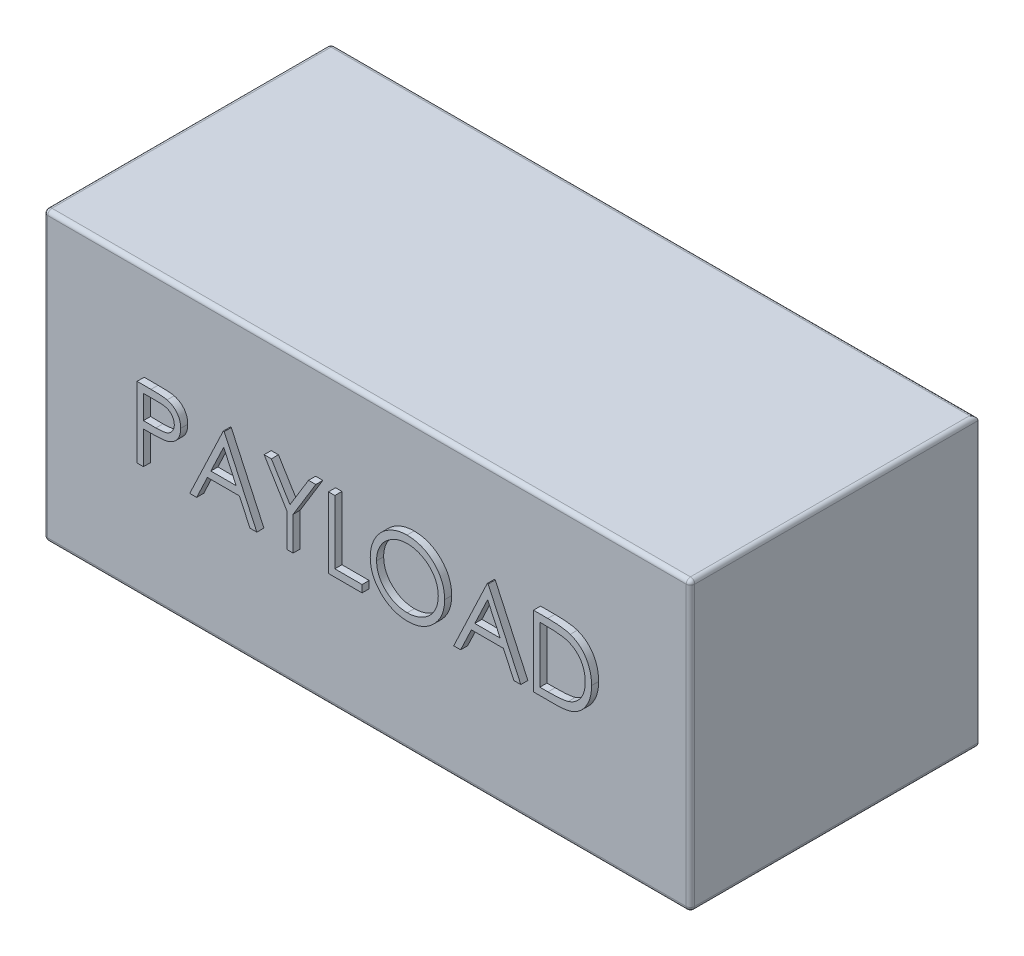
SolidWorks part; units mm, degrees
ref_plane "Front Plane" through (0, 0, 0) normal (0, 0, 1) x (1, 0, 0)
ref_plane "Top Plane" through (0, 0, 0) normal (0, 1, 0) x (1, 0, 0)
ref_plane "Right Plane" through (0, 0, 0) normal (1, 0, 0) x (0, 0, -1)
sketch "Sketch1" plane through (0, 0, 0) normal (0, 0, 1) x (1, 0, 0)
  line L1 (-228.6, -101.6) -> (228.6, -101.6)
  line L2 (-228.6, -101.6) -> (-228.6, 101.6)
  line L3 (-228.6, 101.6) -> (228.6, 101.6)
  line L4 (228.6, -101.6) -> (228.6, 101.6)
  line L5 (0, 101.6) -> (0, -101.6) construction
  line L6 (-228.6, 0) -> (228.6, 0) construction
  point P0 (0, 0)
  dimension "D1" = 457.2
  dimension "D2" = 203.2
extrude "Boss-Extrude1" add sketch "Sketch1" along normal blind 203.2
sketch "Sketch2" plane through (0, -101.6, 0) normal (0, -1, 0) x (1, 0, 0)
  text T0 "PAYLOAD" font "Century Gothic" height 50
extrude "Boss-Extrude2" add sketch "Sketch2" along normal blind 5
sketch "Sketch3" plane through (0, 0, 203.2) normal (0, 0, 1) x (1, 0, 0)
  text T0 "PAYLOAD" font "Century Gothic" height 50
extrude "Boss-Extrude3" add sketch "Sketch3" along normal blind 5
fillet "Fillet1" radius 3 11 edges at (-228.6, 0, 0) (-228.6, 101.6, 101.6) (0, 101.6, 0) (0, 101.6, 203.2) (228.6, 101.6, 101.6) (228.6, 0, 203.2) (228.6, -101.6, 101.6) (0, -101.6, 0) (-228.6, -101.6, 101.6) (-228.6, 0, 203.2) (0, -101.6, 203.2)
